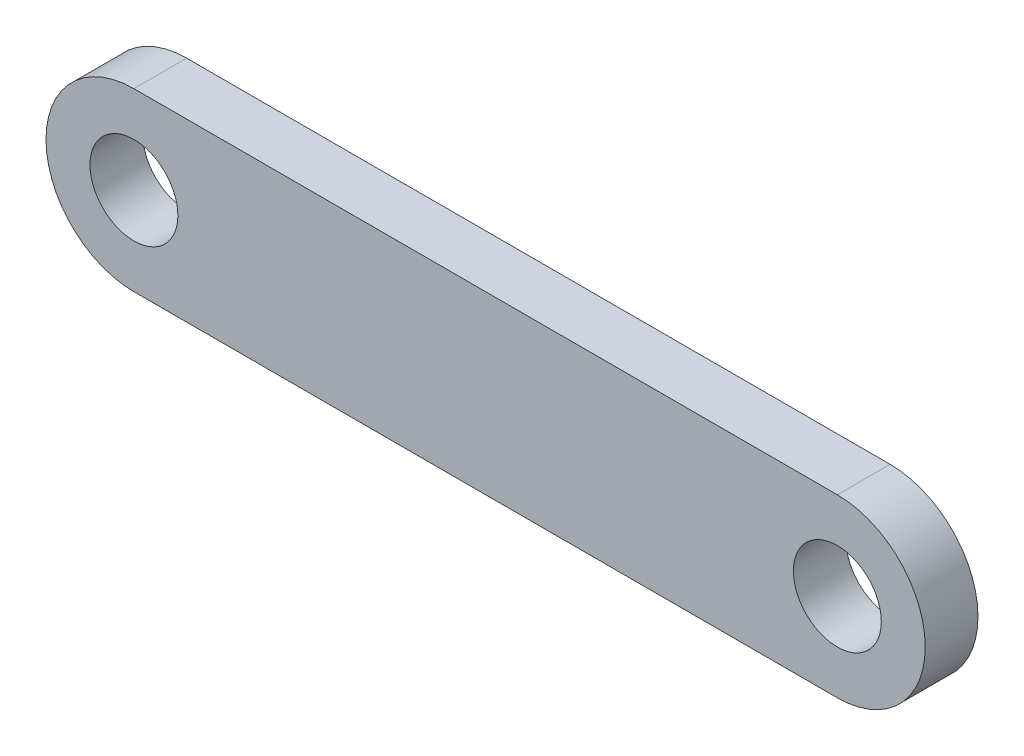
SolidWorks part; units mm, degrees
ref_plane "Спереди" through (0, 0, 0) normal (0, 0, 1) x (1, 0, 0)
ref_plane "Сверху" through (0, 0, 0) normal (0, 1, 0) x (1, 0, 0)
ref_plane "Справа" through (0, 0, 0) normal (1, 0, 0) x (0, 0, -1)
other "Configuration Table"
sketch "Sketch19" plane through (0, 0, 0) normal (0, 0, 1) x (1, 0, 0)
  line L0 (0, -5) -> (0, 5) construction
  line L1 (10, -5) -> (-10, -5)
  line L2 (10, -5) -> (10, 5)
  line L3 (10, 5) -> (-10, 5)
  line L4 (-10, -5) -> (-10, 5)
  line L5 (10, -5) -> (-10, 5) construction
  line L6 (10, 5) -> (-10, -5) construction
  point P0 (0, 0)
  point P6 (0, -5)
  point P8 (0, 5)
  dimension "D1" = 20
  dimension "D2" = 10
extrude "Boss-Extrude4" add sketch "Sketch19" against normal blind 3 contours L3 L4 L1 L2
sketch "Sketch22" plane through (0, 0, 0) normal (0, 0, 1) x (1, 0, 0)
  line L0 (10, 5) -> (20, 5)
  line L2 (10, -5) -> (20, -5)
  line L3 (10, 5) -> (10, -5)
  line L5 (10, -5) -> (10, 5) construction
  arc A0 (20, 5) -> (20, -5) centre (20, 0) cw
  circle A1 centre (20, 0) radius 2.5
  point P8 (0, 0)
  dimension "D1" = 10
  dimension "D2" = 5
ref_plane "Plane13" through (0, 0, 0) normal (0, 0, 1) x (1, 0, 0)
extrude "Boss-Extrude5" add sketch "Sketch22" against normal up to surface (3 mm away) contours L0 A0 L2 L3
ref_plane "Plane14" through (0, 0, 0) normal (-1, 0, 0) x (0, 0, 1)
mirror "Mirror2" about plane through (0, 0, 0) normal (-1, 0, 0) of "Boss-Extrude4", "Boss-Extrude5"
